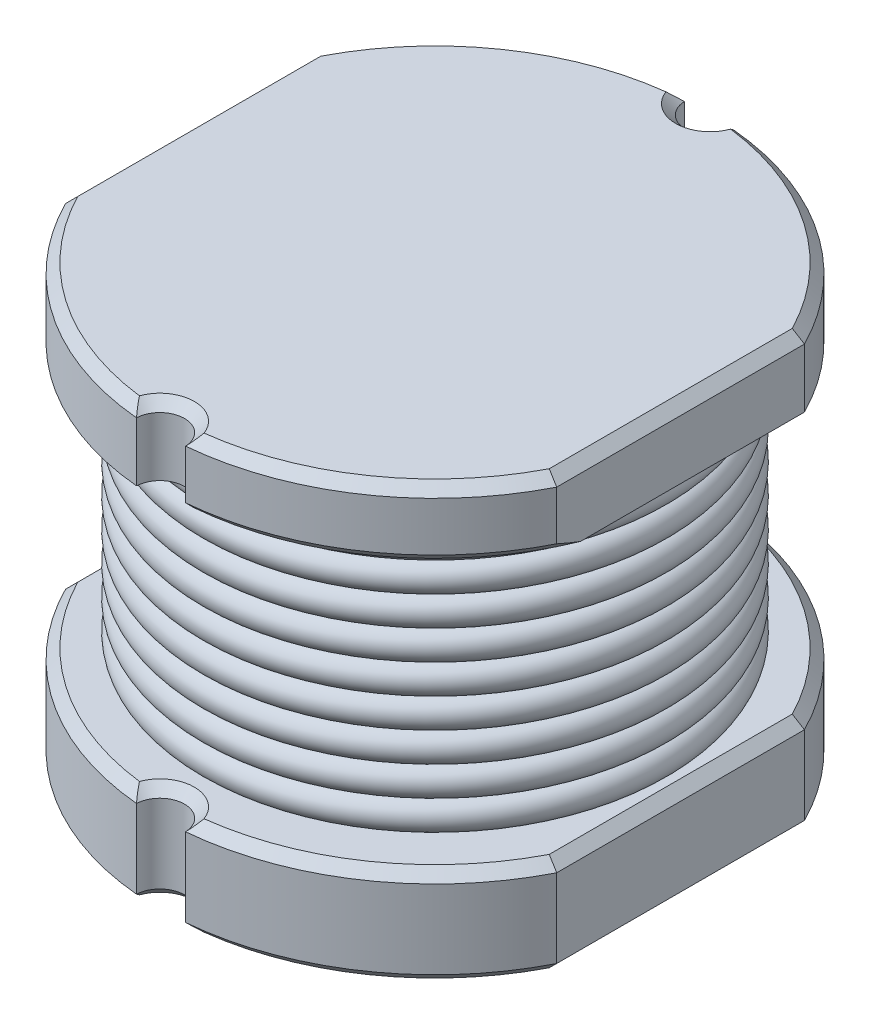
SolidWorks part; units mm, degrees
ref_plane "Front Plane" through (0, 0, 0) normal (0, 0, 1) x (1, 0, 0)
ref_plane "Top Plane" through (0, 0, 0) normal (0, 1, 0) x (1, 0, 0)
ref_plane "Right Plane" through (0, 0, 0) normal (1, 0, 0) x (0, 0, -1)
sketch "Sketch1" plane through (0, 0, 0) normal (0, 1, 0) x (1, 0, 0)
  circle A0 centre (0, 0) radius 2.8
  dimension "D1" = 5.6
extrude "BASE" add sketch "Sketch1" along normal blind 1
sketch "Sketch2" plane through (0, 1, 0) normal (0, 1, 0) x (1, 0, 0)
  circle A0 centre (0, 0) radius 2
  dimension "D1" = 4
extrude "COIL ENCOMPASSMENT" add sketch "Sketch2" along normal blind 2.7
sketch "Sketch3" plane through (0, 3.7, 0) normal (0, 1, 0) x (1, 0, 0)
  circle A0 centre (0, 0) radius 2.8
  dimension "D1" = 5.6
extrude "TOP BASE" add sketch "Sketch3" along normal blind 0.7
sketch "Sketch5" plane through (0, 4.4, 0) normal (0, 1, 0) x (1, 0, 0)
  line L0 (0, -2.8) -> (0, 2.8) construction
  circle A0 centre (0, -2.8) radius 0.25
  circle A1 centre (0, 0) radius 2.8 construction
  circle A2 centre (0, 2.8) radius 0.25
  dimension "D1" = 0.5
extrude "SIDE CUTS FOR BASES" cut sketch "Sketch5" against normal up to surface (4.4 mm away) up to face at (0, 0, 2.8)
sketch "Sketch98" plane through (0, 4.4, 0) normal (0, 1, 0) x (1, 0, 0)
  line L1 (-2.5, -1.261) -> (-2.8, -1.261)
  line L2 (-2.5, -1.261) -> (-2.5, 1.261)
  line L3 (-2.5, 1.261) -> (-2.8, 1.261)
  line L4 (-2.8, -1.261) -> (-2.8, 1.261)
  line L5 (-2.5, -1.261) -> (-2.8, 1.261) construction
  line L6 (-2.5, 1.261) -> (-2.8, -1.261) construction
  arc A0 (-0.2498, 2.7888) -> (-0.2498, -2.7888) centre (0, 0) ccw construction
  dimension "D1" = 2.5
extrude "BASE SIDES" cut sketch "Sketch98" against normal through all
mirror "BS M" about plane through (0, 0, 0) normal (1, 0, 0) of "BASE SIDES"
ref_plane "COIL START" through (0, 1.15, 0) normal (0, 1, 0) x (1, 0, 0)
sketch "Sketch6" plane through (0, 1.15, 0) normal (0, 1, 0) x (1, 0, 0)
  circle A0 centre (0, 0) radius 2.25
  dimension "D1" = 4.5
sweep "COIL" add path "Sketch6" circular profile diameter 0.3 parameters "D3"=0.3
pattern_linear "COIL P" count 10 spacing 0.3 along (0, 1, 0) of "COIL"
chamfer "BASES C" distance 0.1 angle 45 27 edges at (0, 1, 2) (1.5729, 1, 2.3165) (1.5729, 1, -2.3165) (-1.5729, 1, -2.3165) (-1.5729, 1, 2.3165) (0, 1, 2.55) (0, 1, -2.55) (1.5729, 3.7, 2.3165) (-1.5729, 3.7, -2.3165) (0, 0, 2.55) (1.5729, 0, 2.3165) (-1.5729, 0, 2.3165) (0, 0, -2.55) (-1.5729, 0, -2.3165) (1.5729, 0, -2.3165) (1.5729, 4.4, 2.3165) (1.5729, 4.4, -2.3165) (-1.5729, 4.4, -2.3165) (-1.5729, 4.4, 2.3165) (0, 4.4, 2.55) (0, 4.4, -2.55) (-2.5, 4.4, 0) (2.5, 4.4, 0) (-2.5, 0, 0) (2.5, 0, 0) (-2.5, 1, 0) (2.5, 1, 0)
